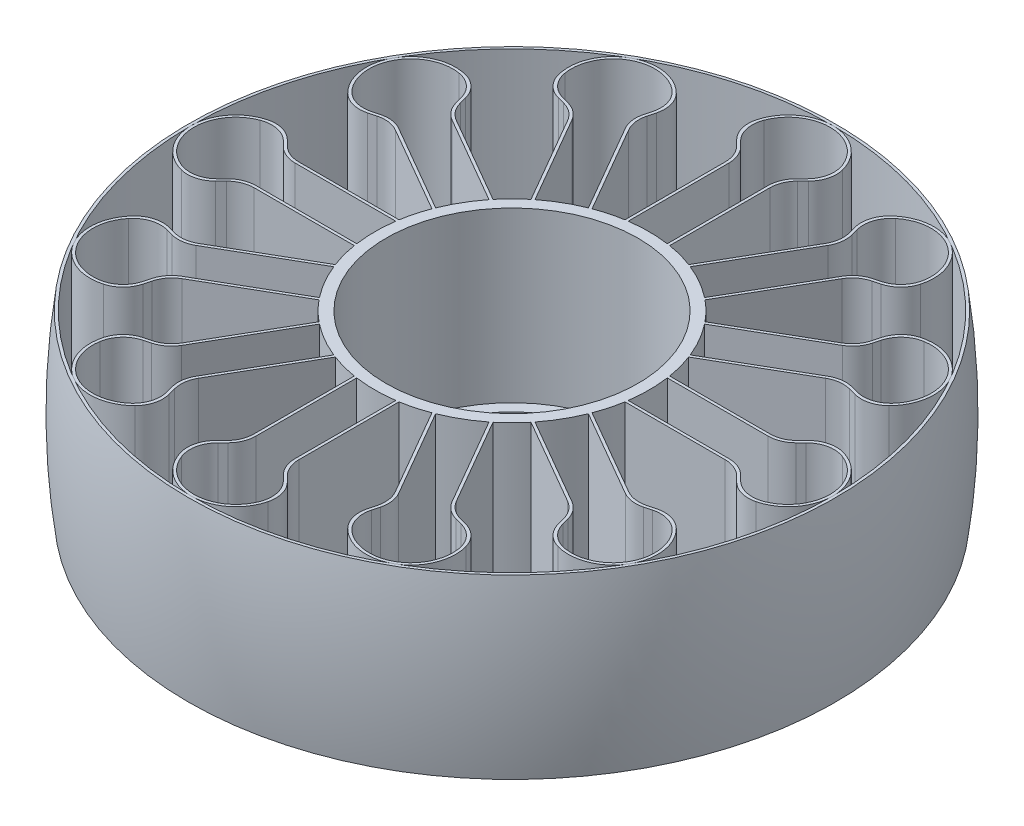
SolidWorks part; units mm, degrees
material "POLYURETHANE (11671)"
ref_plane "Front Plane" through (0, 0, 0) normal (0, 0, 1) x (1, 0, 0)
ref_plane "Top Plane" through (0, 0, 0) normal (0, 1, 0) x (1, 0, 0)
ref_plane "Right Plane" through (0, 0, 0) normal (1, 0, 0) x (0, 0, -1)
sketch "Sketch1" plane through (0, 0, 0) normal (0, 0, 1) x (1, 0, 0)
  line L8 (0, 7.386) -> (0, -6.378) construction
  line L9 (-7.6015, 0) -> (9.1971, 0) construction
  line L10 (20.55, -14.35) -> (22.55, -14.35)
  line L11 (22.55, -14.35) -> (22.55, 15.85)
  line L14 (22.55, 15.85) -> (24.55, 15.85)
  line L16 (24.55, -15.85) -> (20.55, -15.85)
  line L17 (20.55, -15.85) -> (20.55, -14.35)
  line L18 (24.55, 15.85) -> (24.55, -15.85)
other "Pen Sketch1" parameters "D1"=70.898, "D2"=12.5015, "D3"=28.2028, "D4"=34.9, "D5"=3, "D6"=22.6476
revolve "Revolve3" add sketch "Sketch1" angle 360 about L8
sketch "Sketch2" plane through (0, 15.85, 0) normal (0, 1, 0) x (1, 0, 0)
  line L0 (0, 42.3882) -> (0, -40.8923) construction
  line L1 (-4, 24.2219) -> (-4, 44.2219)
  line L2 (-4, 44.2219) -> (-7.8891, 48.111)
  line L3 (7.8891, 48.111) -> (4, 44.2219)
  line L4 (4, 44.2219) -> (4, 24.2219)
  line L5 (-3.5, 24.8043) -> (-3.5, 44.429)
  line L6 (-3.5, 44.429) -> (-7.4205, 48.3496)
  line L7 (7.4205, 48.3496) -> (3.5, 44.429)
  line L8 (3.5, 44.429) -> (3.5, 24.8043)
  line L9 (0.5, 42.3882) -> (0.5, -40.8923)
  line L10 (-3.5, 24.8043) -> (-3.5, 24.2992)
  line L11 (3.5, 24.8043) -> (3.5, 24.2992)
  arc A0 (-4, 24.2219) -> (4, 24.2219) centre (0, 0) cw
  circle A1 centre (0, 0) radius 24.55 construction
  arc A2 (-7.8891, 48.111) -> (7.8891, 48.111) centre (0, 49.4385) cw
  arc A3 (-7.4205, 48.3496) -> (7.4205, 48.3496) centre (0, 49.4385) cw
  arc A5 (-3.5, 24.8043) -> (3.5, 24.8043) centre (0, 0) cw construction
  circle M17 centre (0, 0) radius 24.55
  dimension "D2" = 135
  dimension "D5" = 8
  dimension "D1" = 135
  dimension "D3" = 20
  dimension "D4" = 8
  dimension "D6" = 5.5
  dimension "D7" = 0.5
extrude "Boss-Extrude1" add sketch "Sketch2" against normal up to surface (31.7 mm away) contours L6 A3 L7 L8 L11 L4 L3 A2 L2 L1 L10 L5 M17 up to face at (0, -15.85, 24.55)
fillet "Fillet1" radius 5 8 edges at (-7.8891, 0, -48.111) (-4, 0, -44.2219) (7.8891, 0, -48.111) (4, 0, -44.2219) (7.4205, 0, -48.3496) (3.5, 0, -44.429) (-7.4205, 0, -48.3496) (-3.5, 0, -44.429)
pattern_circular "CirPattern1" count 12 over 360 about axis through (0, 0, 0) along (0, 1, 0) of "Boss-Extrude1", "Fillet1"
sketch "Sketch3" plane through (0, 0, 0) normal (1, 0, 0) x (0, 0, -1)
  line L0 (0, 24.9652) -> (0, -27.7966) construction
  line L4 (57.4385, 15.85) -> (57.4385, -15.85)
  line L5 (57.4385, -15.85) -> (57.9385, -15.85)
  line L6 (57.4385, 15.85) -> (57.9385, 15.85)
  arc A2 (57.9385, 15.85) -> (57.9385, -15.85) centre (-60, 0) cw
  dimension "D1" = 0.5
  dimension "D2" = 60
revolve "Revolve4" add sketch "Sketch3" angle 360 about L0
